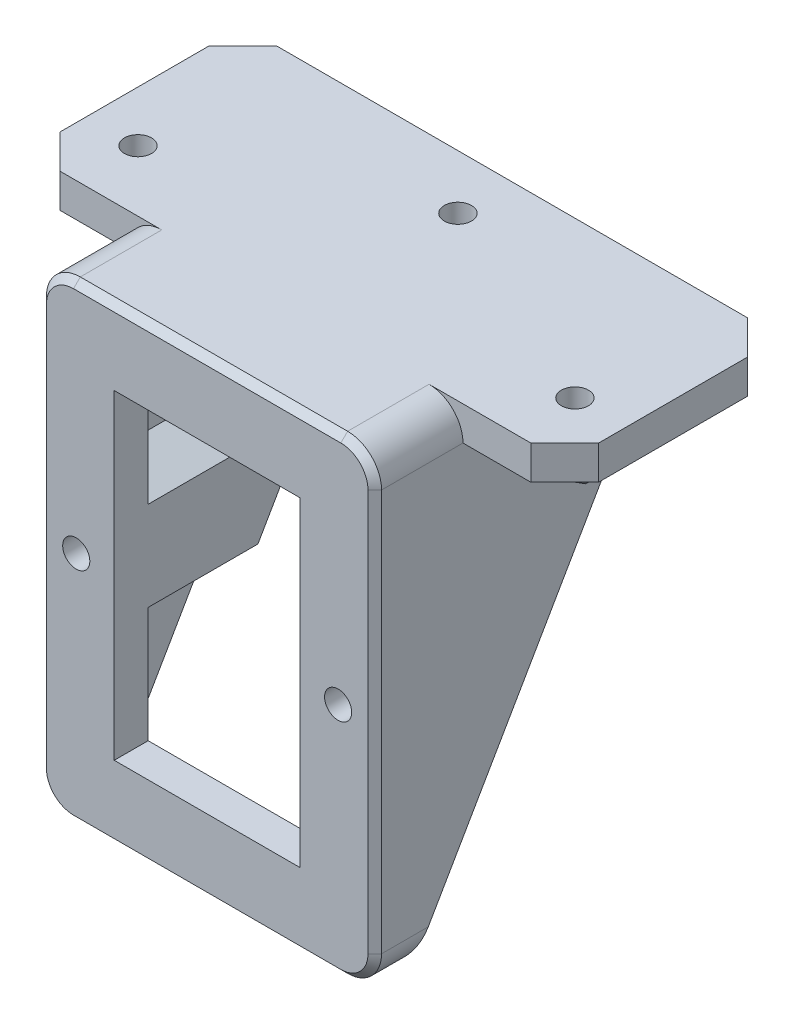
SolidWorks part; units mm, degrees
ref_plane "Front Plane" through (0, 0, 0) normal (0, 0, 1) x (1, 0, 0)
ref_plane "Top Plane" through (0, 0, 0) normal (0, 1, 0) x (1, 0, 0)
ref_plane "Right Plane" through (0, 0, 0) normal (1, 0, 0) x (0, 0, -1)
sketch "Sketch1" plane through (0, 0, 0) normal (0, 0, 1) x (1, 0, 0)
  line L0 (-36.4532, 0) -> (46.6601, 0) construction
  line L1 (-13.5, 23.4) -> (13.5, 23.4) construction
  line L2 (-13.5, 23.4) -> (-13.5, -23.4) construction
  line L3 (-13.5, -23.4) -> (13.5, -23.4) construction
  line L4 (13.5, 23.4) -> (13.5, -23.4) construction
  line L5 (0, 29.9068) -> (0, -40.6544) construction
  line L6 (-13.7, 23.6) -> (13.7, 23.6)
  line L7 (13.7, 23.6) -> (13.7, -23.6)
  line L8 (-13.7, -23.6) -> (13.7, -23.6)
  line L9 (-13.7, 23.6) -> (-13.7, -23.6)
  line L10 (-24.7, 34.6) -> (-24.7, -34.6)
  line L11 (-24.7, -34.6) -> (24.7, -34.6)
  line L12 (24.7, 34.6) -> (24.7, -34.6)
  line L13 (-24.7, 34.6) -> (24.7, 34.6)
  dimension "D1" = 46.8
  dimension "D2" = 27
  dimension "D3" = 0.2
  dimension "D4" = 11
extrude "Boss-Extrude1" add sketch "Sketch1" against normal blind 5
sketch "Sketch2" plane through (0, 0, 0) normal (0, 0, 1) x (1, 0, 0)
  line L0 (13.7, -23.6) -> (13.7, 23.6) construction
  line L1 (0, 0) -> (0, 17.0969) construction
  circle A0 centre (19.3, 0) radius 2
  circle A1 centre (-19.3, 0) radius 2
  dimension "D1" = 4
  dimension "D2" = 5.6
extrude "Cut-Extrude1" cut sketch "Sketch2" against normal blind 15
sketch "Sketch4" plane through (24.7, 0, 0) normal (1, 0, 0) x (0, 0, -1)
  line L0 (5, 34.6) -> (44.9526, 34.6)
  line L4 (44.9526, 34.6) -> (5, -34.6)
  line L5 (5, -34.6) -> (5, 34.6) construction
  line L6 (5, -34.6) -> (5, 34.6)
  line L7 (5, -34.6) -> (0, -34.6) construction
  dimension "D1" = 30
extrude "Boss-Extrude2" add sketch "Sketch4" against normal up to vertex (49.4 mm away)
sketch "Sketch3" plane through (0, 0, -5) normal (0, 0, -1) x (-1, 0, 0)
  line L1 (-19.3, -4.0415) -> (-15.8, -2.0207)
  line L2 (-15.8, -2.0207) -> (-15.8, 2.0207)
  line L3 (-15.8, 2.0207) -> (-19.3, 4.0415)
  line L4 (-19.3, 4.0415) -> (-22.8, 2.0207)
  line L5 (-22.8, 2.0207) -> (-22.8, -2.0207)
  line L6 (-22.8, -2.0207) -> (-19.3, -4.0415)
  line L7 (19.3, -4.0415) -> (22.8, -2.0207)
  line L8 (22.8, -2.0207) -> (22.8, 2.0207)
  line L9 (22.8, 2.0207) -> (19.3, 4.0415)
  line L10 (19.3, 4.0415) -> (15.8, 2.0207)
  line L11 (15.8, 2.0207) -> (15.8, -2.0207)
  line L12 (15.8, -2.0207) -> (19.3, -4.0415)
  circle A0 centre (-19.3, 0) radius 3.5 construction
  circle A1 centre (19.3, 0) radius 3.5 construction
  dimension "D1" = 7
extrude "Cut-Extrude2" cut sketch "Sketch3" along normal through all
sketch "Sketch5" plane through (0, 0, -5) normal (0, 0, 1) x (1, 0, 0)
  line L4 (-13.7, 23.6) -> (-13.7, -23.6)
  line L5 (-13.7, -23.6) -> (13.7, -23.6)
  line L6 (13.7, -23.6) -> (13.7, 23.6)
  line L7 (13.7, 23.6) -> (-13.7, 23.6)
  line L8 (-13.7, 23.6) -> (-13.7, -23.6)
  line L9 (-13.7, -23.6) -> (13.7, -23.6)
  line L10 (13.7, -23.6) -> (13.7, 23.6)
  line L11 (13.7, 23.6) -> (-13.7, 23.6)
  dimension "D1" = 0
extrude "Cut-Extrude3" cut sketch "Sketch5" against normal blind 93
sketch "Sketch6" plane through (0, 0, 0) normal (0, 0, 1) x (1, 0, 0)
  line L0 (19.7, 29.6) -> (-19.7, 29.6)
  line L1 (-19.7, 29.6) -> (-19.7, 10.0459)
  line L2 (-19.7, -34.6) -> (19.7, -34.6)
  line L3 (19.7, -34.6) -> (19.7, -10.0459)
  line L4 (24.7, 34.6) -> (-24.7, 34.6)
  line L5 (-24.7, 34.6) -> (-24.7, -34.6)
  line L6 (-24.7, -34.6) -> (24.7, -34.6)
  line L7 (24.7, -34.6) -> (24.7, 34.6)
  line L8 (24.7, 34.6) -> (-24.7, 34.6) construction
  line L9 (22.8, -2.0207) -> (19.3, -4.0415) construction
  line L10 (-24.7, -34.6) -> (24.7, -34.6) construction
  line L11 (24.7, -6.6973) -> (24.7, 34.6) construction
  line L24 (-15.8, -2.0207) -> (-19.3, -4.0415) construction
  line L25 (-19.3, -4.0415) -> (-22.8, -2.0207) construction
  line L26 (-22.8, -2.0207) -> (-22.8, 2.0207) construction
  line L27 (-22.8, 2.0207) -> (-19.3, 4.0415) construction
  line L28 (-19.3, 4.0415) -> (-15.8, 2.0207) construction
  line L29 (-15.8, 2.0207) -> (-15.8, -2.0207) construction
  line L30 (22.8, -2.0207) -> (19.3, -4.0415) construction
  line L31 (19.3, -4.0415) -> (15.8, -2.0207) construction
  line L32 (15.8, -2.0207) -> (15.8, 2.0207) construction
  line L33 (15.8, 2.0207) -> (19.3, 4.0415) construction
  line L34 (19.3, 4.0415) -> (22.8, 2.0207) construction
  line L35 (22.8, 2.0207) -> (22.8, -2.0207) construction
  line L36 (-19.7, 10.0459) -> (-10.8, 4.9075)
  line L37 (-10.8, 4.9075) -> (-10.8, -4.9075)
  line L38 (-10.8, -4.9075) -> (-19.7, -10.0459)
  line L39 (19.3, 9.815) -> (27.8, 4.9075) construction
  line L40 (19.7, 10.0459) -> (19.7, 29.6)
  line L41 (19.7, -29.6) -> (19.7, 29.6) construction
  line L42 (10.8, 4.9075) -> (19.7, 10.0459)
  line L43 (19.3, -9.815) -> (10.8, -4.9075) construction
  line L44 (22.8, 2.0207) -> (22.8, -2.0207) construction
  line L45 (19.3, 4.0415) -> (22.8, 2.0207) construction
  line L46 (19.7, -10.0459) -> (10.8, -4.9075)
  line L47 (10.8, -4.9075) -> (10.8, 4.9075)
  line L48 (-19.7, -10.0459) -> (-19.7, -34.6)
  line L49 (-19.7, 29.6) -> (-19.7, -29.6) construction
  line L50 (-10.8, -4.9075) -> (-19.3, -9.815) construction
  line L51 (-27.8, 4.9075) -> (-19.3, 9.815) construction
  line L52 (-19.3, 9.815) -> (-10.8, 4.9075) construction
  line L53 (-19.3, -9.815) -> (-27.8, -4.9075) construction
  line L54 (10.8, 4.9075) -> (19.3, 9.815) construction
  line L55 (-24.7, 34.6) -> (-24.7, -34.6) construction
  line L56 (-27.8, -4.9075) -> (-27.8, 4.9075) construction
  line L57 (15.8, 2.0207) -> (19.3, 4.0415) construction
  line L58 (27.8, -4.9075) -> (19.3, -9.815) construction
  line L59 (15.8, -2.0207) -> (15.8, 2.0207) construction
  line L60 (24.7, -34.6) -> (24.7, 34.6) construction
  line L61 (27.8, 4.9075) -> (27.8, -4.9075) construction
  line L62 (-19.7, -29.6) -> (19.7, -29.6) construction
  line L63 (19.3, -4.0415) -> (15.8, -2.0207) construction
  line L64 (-22.8, -2.0207) -> (-22.8, 2.0207) construction
  line L65 (-22.8, 2.0207) -> (-19.3, 4.0415) construction
  line L66 (-19.3, 4.0415) -> (-15.8, 2.0207) construction
  line L67 (-15.8, 2.0207) -> (-15.8, -2.0207) construction
  line L68 (-15.8, -2.0207) -> (-19.3, -4.0415) construction
  line L69 (-19.3, -4.0415) -> (-22.8, -2.0207) construction
  dimension "D1" = 0
  dimension "D2" = 5
  dimension "D3" = 5
  dimension "D4" = 5
extrude "Cut-Extrude4" cut sketch "Sketch6" against normal blind 93 from offset 5 offset against normal yes
sketch "Sketch7" plane through (0, 34.6, 0) normal (0, 1, 0) x (1, 0, 0)
  line L0 (24.7, 0) -> (-24.7, 0) construction
  line L1 (-39.7, 44.9526) -> (39.7, 44.9526)
  line L2 (-39.7, 44.9526) -> (-39.7, 0)
  line L3 (-39.7, 0) -> (39.7, 0)
  line L4 (39.7, 44.9526) -> (39.7, 0)
  line L5 (-24.7, 44.9526) -> (24.7, 44.9526) construction
  line L6 (-24.7, 44.9526) -> (-24.7, 0) construction
  line L8 (0, 0) -> (0, 55.3404) construction
  dimension "D1" = 15
extrude "Boss-Extrude3" add sketch "Sketch7" against normal blind 5
sketch "Sketch8" plane through (0, 29.6, 0) normal (0, -1, 0) x (1, 0, 0)
  line L1 (-3.5, -34.9319) -> (-3.5, -38.9734)
  line L2 (-3.5, -38.9734) -> (0, -40.9941)
  line L3 (0, -40.9941) -> (3.5, -38.9734)
  line L4 (3.5, -38.9734) -> (3.5, -34.9319)
  line L5 (3.5, -34.9319) -> (0, -32.9112)
  line L6 (0, -32.9112) -> (-3.5, -34.9319)
  line L7 (-32.2, -17.9585) -> (-35.7, -19.9793)
  line L8 (-35.7, -19.9793) -> (-35.7, -24.0207)
  line L9 (-35.7, -24.0207) -> (-32.2, -26.0415)
  line L10 (-32.2, -26.0415) -> (-28.7, -24.0207)
  line L11 (-28.7, -24.0207) -> (-28.7, -19.9793)
  line L12 (-28.7, -19.9793) -> (-32.2, -17.9585)
  line L13 (32.2, -17.9585) -> (28.7, -19.9793)
  line L14 (28.7, -19.9793) -> (28.7, -24.0207)
  line L15 (28.7, -24.0207) -> (32.2, -26.0415)
  line L16 (32.2, -26.0415) -> (35.7, -24.0207)
  line L17 (35.7, -24.0207) -> (35.7, -19.9793)
  line L18 (35.7, -19.9793) -> (32.2, -17.9585)
  line L30 (25.7, -25.7528) -> (32.2, -29.5056)
  line L31 (32.2, -29.5056) -> (38.7, -25.7528)
  line L32 (38.7, -25.7528) -> (38.7, -18.2472)
  line L33 (38.7, -18.2472) -> (32.2, -14.4944)
  line L34 (32.2, -14.4944) -> (25.7, -18.2472)
  line L35 (25.7, -18.2472) -> (25.7, -25.7528)
  line L36 (32.2, 0) -> (32.2, -44.9526) construction
  line L37 (24.7, 0) -> (39.7, 0) construction
  line L38 (39.7, -44.9526) -> (-39.7, -44.9526) construction
  line L39 (0, 0) -> (0, -56.5255) construction
  line L40 (-39.7, 0) -> (-24.7, 0) construction
  line L41 (-32.2, -14.4944) -> (-38.7, -18.2472)
  line L42 (-38.7, -18.2472) -> (-38.7, -25.7528)
  line L43 (-38.7, -25.7528) -> (-32.2, -29.5056)
  line L44 (-32.2, -29.5056) -> (-25.7, -25.7528)
  line L45 (-25.7, -25.7528) -> (-25.7, -18.2472)
  line L46 (-25.7, -18.2472) -> (-32.2, -14.4944)
  line L47 (0, -29.4471) -> (-6.5, -33.1999)
  line L48 (-6.5, -33.1999) -> (-6.5, -40.7054)
  line L49 (-6.5, -40.7054) -> (0, -44.4582)
  line L50 (0, -44.4582) -> (6.5, -40.7054)
  line L51 (6.5, -40.7054) -> (6.5, -33.1999)
  line L52 (6.5, -33.1999) -> (0, -29.4471)
  circle A0 centre (0, -36.9526) radius 3.5 construction
  circle A1 centre (-32.2, -22) radius 3.5 construction
  circle A2 centre (32.2, -22) radius 3.5 construction
  circle A3 centre (-32.2, -22) radius 6.5 construction
  circle A4 centre (0, -36.9526) radius 6.5 construction
  point P55 (-32.2, 0)
  dimension "D1" = 7
  dimension "D5" = 3
  dimension "D3" = 22
  dimension "D4" = 8
  dimension "D2" = 3
extrude "Boss-Extrude4" add sketch "Sketch8" along normal blind 3
sketch "Sketch9" plane through (0, 29.6, 0) normal (0, -1, 0) x (1, 0, 0)
  line L0 (3.5, -34.9319) -> (0, -32.9112) construction
  line L1 (0, -32.9112) -> (-3.5, -34.9319) construction
  line L2 (-3.5, -34.9319) -> (-3.5, -38.9734) construction
  line L3 (-3.5, -38.9734) -> (0, -40.9941) construction
  line L4 (0, -40.9941) -> (3.5, -38.9734) construction
  line L5 (3.5, -38.9734) -> (3.5, -34.9319) construction
  line L6 (35.7, -24.0207) -> (35.7, -19.9793)
  line L7 (35.7, -19.9793) -> (32.2, -17.9585)
  line L8 (32.2, -17.9585) -> (28.7, -19.9793)
  line L9 (28.7, -19.9793) -> (28.7, -24.0207)
  line L10 (28.7, -24.0207) -> (32.2, -26.0415)
  line L11 (32.2, -26.0415) -> (35.7, -24.0207)
  line L12 (35.7, -24.0207) -> (35.7, -19.9793)
  line L13 (35.7, -19.9793) -> (32.2, -17.9585)
  line L14 (32.2, -17.9585) -> (28.7, -19.9793)
  line L15 (28.7, -19.9793) -> (28.7, -24.0207)
  line L16 (28.7, -24.0207) -> (32.2, -26.0415)
  line L17 (32.2, -26.0415) -> (35.7, -24.0207)
  line L18 (-28.7, -24.0207) -> (-28.7, -19.9793) construction
  line L19 (-28.7, -19.9793) -> (-32.2, -17.9585) construction
  line L20 (-32.2, -17.9585) -> (-35.7, -19.9793) construction
  line L21 (-35.7, -19.9793) -> (-35.7, -24.0207) construction
  line L22 (-35.7, -24.0207) -> (-32.2, -26.0415) construction
  line L23 (-32.2, -26.0415) -> (-28.7, -24.0207) construction
  line L24 (3.5, -34.9319) -> (0, -32.9112)
  line L25 (0, -32.9112) -> (-3.5, -34.9319)
  line L26 (-3.5, -34.9319) -> (-3.5, -38.9734)
  line L27 (-3.5, -38.9734) -> (0, -40.9941)
  line L28 (0, -40.9941) -> (3.5, -38.9734)
  line L29 (3.5, -38.9734) -> (3.5, -34.9319)
  line L30 (-28.7, -24.0207) -> (-28.7, -19.9793)
  line L31 (-28.7, -19.9793) -> (-32.2, -17.9585)
  line L32 (-32.2, -17.9585) -> (-35.7, -19.9793)
  line L33 (-35.7, -19.9793) -> (-35.7, -24.0207)
  line L34 (-35.7, -24.0207) -> (-32.2, -26.0415)
  line L35 (-32.2, -26.0415) -> (-28.7, -24.0207)
  dimension "D1" = 0
extrude "Cut-Extrude5" cut sketch "Sketch9" against normal blind 1
sketch "Sketch10" plane through (0, 30.6, 0) normal (0, -1, 0) x (1, 0, 0)
  line L0 (24.7, 0) -> (39.7, 0) construction
  line L1 (-3.5, -34.9319) -> (-3.5, -38.9734) construction
  line L2 (-35.7, -19.9793) -> (-35.7, -24.0207) construction
  circle A0 centre (32.2, -22) radius 2
  circle A1 centre (0, -36.9526) radius 2
  circle A2 centre (-32.2, -22) radius 2
  point P4 (32.2, 0)
  point P9 (-3.5, -36.9526)
  point P16 (-35.7, -22)
  dimension "D1" = 4
  dimension "D2" = 22
extrude "Cut-Extrude6" cut sketch "Sketch10" against normal through all
sketch "Sketch11" plane through (0, 0, 0) normal (0, 0, 1) x (1, 0, 0)
  line L0 (39.7, 34.6) -> (-39.7, 34.6) construction
  line L1 (24.7, 29.6) -> (39.7, 29.6)
  line L2 (24.7, 29.6) -> (24.7, 34.6)
  line L3 (24.7, 34.6) -> (39.7, 34.6)
  line L4 (39.7, 29.6) -> (39.7, 34.6)
  line L5 (-24.7, 29.6) -> (-39.7, 29.6)
  line L6 (-24.7, 29.6) -> (-24.7, 34.6)
  line L7 (-24.7, 34.6) -> (-39.7, 34.6)
  line L8 (-39.7, 29.6) -> (-39.7, 34.6)
  line L9 (-39.7, 29.6) -> (-39.7, 34.6) construction
extrude "Cut-Extrude7" cut sketch "Sketch11" against normal blind 13
chamfer "Chamfer1" distance 2.75 angle 45 18 edges at (-25.7, 26.6, -22) (-28.95, 26.6, -27.6292) (-35.45, 26.6, -27.6292) (-38.7, 26.6, -22) (-35.45, 26.6, -16.3708) (-28.95, 26.6, -16.3708) (6.5, 26.6, -36.9526) (3.25, 26.6, -42.5818) (-3.25, 26.6, -42.5818) (-6.5, 26.6, -36.9526) (-3.25, 26.6, -31.3235) (3.25, 26.6, -31.3235) (28.95, 26.6, -16.3708) (35.45, 26.6, -16.3708) (38.7, 26.6, -22) (35.45, 26.6, -27.6292) (28.95, 26.6, -27.6292) (25.7, 26.6, -22)
sketch "Sketch12" plane through (0, 26.6, 0) normal (0, -1, 0) x (1, 0, 0)
  line L21 (3.5, -38.9734) -> (3.5, -34.9319) construction
  line L22 (3.5, -34.9319) -> (0, -32.9112) construction
  line L23 (0, -32.9112) -> (-3.5, -34.9319) construction
  line L24 (-3.5, -34.9319) -> (-3.5, -38.9734) construction
  line L25 (-3.5, -38.9734) -> (0, -40.9941) construction
  line L26 (0, -40.9941) -> (3.5, -38.9734) construction
  line L27 (35.45, -20.1236) -> (32.2, -18.2472)
  line L28 (32.2, -18.2472) -> (28.95, -20.1236)
  line L29 (28.95, -20.1236) -> (28.95, -23.8764)
  line L30 (28.95, -23.8764) -> (32.2, -25.7528)
  line L31 (35.45, -23.8764) -> (35.45, -20.1236)
  line L32 (32.2, -25.7528) -> (35.45, -23.8764)
  line L33 (35.45, -20.1236) -> (32.2, -18.2472)
  line L34 (32.2, -18.2472) -> (28.95, -20.1236)
  line L35 (28.95, -20.1236) -> (28.95, -23.8764)
  line L36 (28.95, -23.8764) -> (32.2, -25.7528)
  line L37 (35.45, -23.8764) -> (35.45, -20.1236)
  line L38 (32.2, -25.7528) -> (35.45, -23.8764)
  line L39 (32.2, -26.0415) -> (35.7, -24.0207)
  line L40 (35.7, -24.0207) -> (35.7, -19.9793)
  line L41 (35.7, -19.9793) -> (32.2, -17.9585)
  line L42 (32.2, -17.9585) -> (28.7, -19.9793)
  line L43 (28.7, -19.9793) -> (28.7, -24.0207)
  line L44 (28.7, -24.0207) -> (32.2, -26.0415)
  line L45 (32.2, -26.0415) -> (35.7, -24.0207)
  line L46 (35.7, -24.0207) -> (35.7, -19.9793)
  line L47 (35.7, -19.9793) -> (32.2, -17.9585)
  line L48 (32.2, -17.9585) -> (28.7, -19.9793)
  line L49 (28.7, -19.9793) -> (28.7, -24.0207)
  line L50 (28.7, -24.0207) -> (32.2, -26.0415)
  line L51 (-32.2, -26.0415) -> (-28.7, -24.0207) construction
  line L52 (-28.7, -24.0207) -> (-28.7, -19.9793) construction
  line L53 (-28.7, -19.9793) -> (-32.2, -17.9585) construction
  line L54 (-32.2, -17.9585) -> (-35.7, -19.9793) construction
  line L55 (-35.7, -19.9793) -> (-35.7, -24.0207) construction
  line L56 (-35.7, -24.0207) -> (-32.2, -26.0415) construction
  line L57 (3.5, -38.9734) -> (3.5, -34.9319)
  line L58 (3.5, -34.9319) -> (0, -32.9112)
  line L59 (0, -32.9112) -> (-3.5, -34.9319)
  line L60 (-3.5, -34.9319) -> (-3.5, -38.9734)
  line L61 (-3.5, -38.9734) -> (0, -40.9941)
  line L62 (0, -40.9941) -> (3.5, -38.9734)
  line L63 (-32.2, -26.0415) -> (-28.7, -24.0207)
  line L64 (-28.7, -24.0207) -> (-28.7, -19.9793)
  line L65 (-28.7, -19.9793) -> (-32.2, -17.9585)
  line L66 (-32.2, -17.9585) -> (-35.7, -19.9793)
  line L67 (-35.7, -19.9793) -> (-35.7, -24.0207)
  line L68 (-35.7, -24.0207) -> (-32.2, -26.0415)
  line L69 (-3.25, -38.829) -> (0, -40.7054)
  line L70 (0, -40.7054) -> (3.25, -38.829)
  line L71 (3.25, -38.829) -> (3.25, -35.0763)
  line L72 (3.25, -35.0763) -> (0, -33.1999)
  line L73 (0, -33.1999) -> (-3.25, -35.0763)
  line L74 (-3.25, -35.0763) -> (-3.25, -38.829)
  line L75 (-35.45, -23.8764) -> (-32.2, -25.7528)
  line L76 (-32.2, -25.7528) -> (-28.95, -23.8764)
  line L77 (-28.95, -23.8764) -> (-28.95, -20.1236)
  line L78 (-28.95, -20.1236) -> (-32.2, -18.2472)
  line L79 (-32.2, -18.2472) -> (-35.45, -20.1236)
  line L80 (-35.45, -20.1236) -> (-35.45, -23.8764)
  dimension "D1" = 0.25
  dimension "D2" = 0
  dimension "D3" = 0.25
  dimension "D4" = 0.25
extrude "Boss-Extrude5" add sketch "Sketch12" against normal blind 0.5
chamfer "Chamfer2" distance 0.25 angle 45 18 edges at (33.825, 26.6, -19.1854) (30.575, 26.6, -19.1854) (28.95, 26.6, -22) (30.575, 26.6, -24.8146) (33.825, 26.6, -24.8146) (35.45, 26.6, -22) (-33.825, 26.6, -24.8146) (-30.575, 26.6, -24.8146) (-28.95, 26.6, -22) (-30.575, 26.6, -19.1854) (-33.825, 26.6, -19.1854) (-35.45, 26.6, -22) (-1.625, 26.6, -39.7672) (1.625, 26.6, -39.7672) (3.25, 26.6, -36.9526) (1.625, 26.6, -34.1381) (-1.625, 26.6, -34.1381) (-3.25, 26.6, -36.9526)
fillet "Fillet1" radius 5 4 edges at (24.7, -34.6, -2.5) (-24.7, -34.6, -2.5) (-24.7, 34.6, -6.5) (24.7, 34.6, -6.5)
chamfer "Chamfer3" distance 1 angle 45 8 edges at (24.7, 0, 0) (0, -34.6, 0) (-24.7, 0, 0) (0, 34.6, 0) (-23.2355, -33.1355, 0) (-23.2355, 33.1355, 0) (23.2355, 33.1355, 0) (23.2355, -33.1355, 0)
chamfer "Chamfer4" distance 5 angle 45 4 edges at (-39.7, 32.1, -44.9526) (-39.7, 32.1, -13) (39.7, 32.1, -44.9526) (39.7, 32.1, -13)
equation "\"D5@Sketch8\"=\"D2@Sketch8\""
equation "\"D2@Sketch10\"=\"D3@Sketch8\""
equation "\"D4@Sketch12\"=\"D1@Sketch12\""
equation "\"D3@Sketch12\"=\"D1@Sketch12\""
